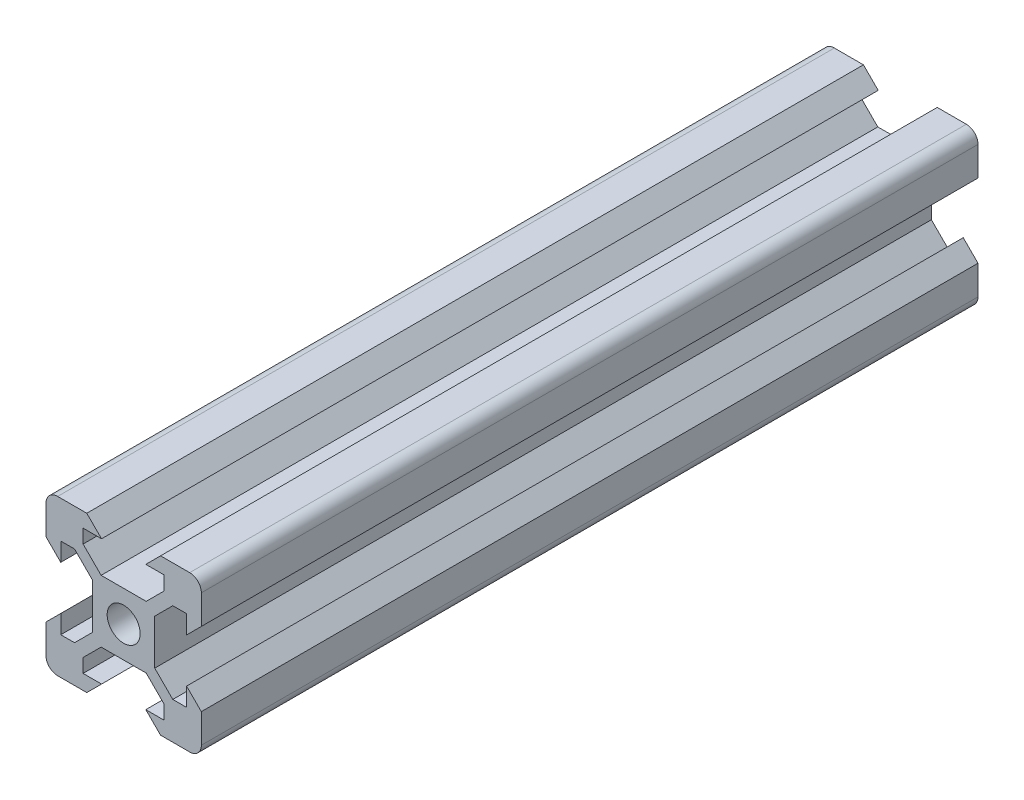
SolidWorks part; units mm, degrees
ref_plane "Front Plane" through (0, 0, 0) normal (0, 0, 1) x (1, 0, 0)
ref_plane "Top Plane" through (0, 0, 0) normal (0, 1, 0) x (1, 0, 0)
ref_plane "Right Plane" through (0, 0, 0) normal (1, 0, 0) x (0, 0, -1)
sketch "Sketch1" plane through (0, 0, 0) normal (0, 0, 1) x (1, 0, 0)
  line L0 (15.6876, 55.3211) -> (115.0437, 55.3211) construction
  line L1 (8.1, 5.225) -> (8.1, 2.85)
  line L2 (-8.5, 10) -> (-4.75, 10)
  line L3 (-10, 8.5) -> (-10, 4.75)
  line L4 (-8.5, -10) -> (-4.75, -10)
  line L5 (10, 8.5) -> (10, 4.75)
  line L6 (6.325, 5.225) -> (4, 2.9)
  line L7 (-8.1, -2.85) -> (-8.1, -5.225)
  line L8 (-2.9, 4) -> (2.9, 4)
  line L9 (-4, 2.9) -> (-4, -2.9)
  line L10 (-2.9, -4) -> (2.9, -4)
  line L11 (4, 2.9) -> (4, -2.9)
  line L12 (2.85, -8.1) -> (5.225, -8.1)
  line L13 (-5.225, -8.1) -> (-2.85, -8.1)
  line L14 (5.225, 6.325) -> (2.9, 4)
  line L17 (-10, 4.75) -> (-8.1, 2.85)
  line L20 (4.75, -10) -> (8.5, -10)
  line L22 (-10, -4.75) -> (-10, -8.5)
  line L23 (10, -4.75) -> (10, -8.5)
  line L24 (-10, -4.75) -> (-8.1, -2.85)
  line L25 (-4.75, -10) -> (-2.85, -8.1)
  line L26 (4.75, -10) -> (2.85, -8.1)
  line L27 (10, -4.75) -> (8.1, -2.85)
  line L28 (10, 4.75) -> (8.1, 2.85)
  line L29 (-4.75, 10) -> (-2.85, 8.1)
  line L30 (4.75, 10) -> (2.85, 8.1)
  line L31 (8.1, -2.85) -> (8.1, -5.225)
  line L32 (6.325, -5.225) -> (8.1, -5.225)
  line L33 (5.225, -6.325) -> (5.225, -8.1)
  line L34 (4.75, 10) -> (8.5, 10)
  line L35 (2.85, 8.1) -> (5.225, 8.1)
  line L36 (10, -10) -> (10.975, -10.975) construction
  line L37 (-5.225, 8.1) -> (-2.85, 8.1)
  line L38 (-8.1, -5.225) -> (-6.325, -5.225)
  line L39 (-5.225, 6.325) -> (-2.9, 4)
  line L40 (-8.1, 5.225) -> (-8.1, 2.85)
  line L41 (-5.225, -6.325) -> (-5.225, -8.1)
  line L42 (-6.325, 5.225) -> (-4, 2.9)
  line L46 (-8.1, 5.225) -> (-6.325, 5.225)
  line L47 (-5.225, 8.1) -> (-5.225, 6.325)
  line L52 (8.1, 5.225) -> (6.325, 5.225)
  line L53 (5.225, 8.1) -> (5.225, 6.325)
  line L63 (4, -2.9) -> (6.325, -5.225)
  line L66 (2.9, -4) -> (5.225, -6.325)
  line L67 (-2.9, -4) -> (-5.225, -6.325)
  line L70 (-4, -2.9) -> (-6.325, -5.225)
  arc A0 (-8.5, -10) -> (-10, -8.5) centre (-8.5, -8.5) cw
  arc A1 (8.5, -10) -> (10, -8.5) centre (8.5, -8.5) ccw
  arc A2 (10, 8.5) -> (8.5, 10) centre (8.5, 8.5) ccw
  arc A3 (-8.5, 10) -> (-10, 8.5) centre (-8.5, 8.5) ccw
  circle A4 centre (0, 0) radius 2.125
  point P2 (0, 0)
  point P8 (0, 0)
  point P14 (-10, -10)
  point P20 (0, 0)
  point P49 (10, 10)
  point P52 (-10, 10)
  dimension "D3" = 1.5
  dimension "D4" = 4.25
  dimension "D1" = 20
  dimension "D2" = 20
  dimension "D13" = 5.25
  dimension "D14" = 5.25
  dimension "D15" = 90
  dimension "D16" = 5.25
  dimension "D17" = 5.25
  dimension "D18" = 5.25
  dimension "D19" = 5.25
  dimension "D20" = 5.25
  dimension "D21" = 5.25
  dimension "D22" = 90
  dimension "D23" = 90
  dimension "D24" = 90
  dimension "D25" = 2.85
  dimension "D26" = 2.85
  dimension "D27" = 2.85
  dimension "D28" = 2.85
extrude "Boss-Extrude1" add sketch "Sketch1" along normal blind 100
